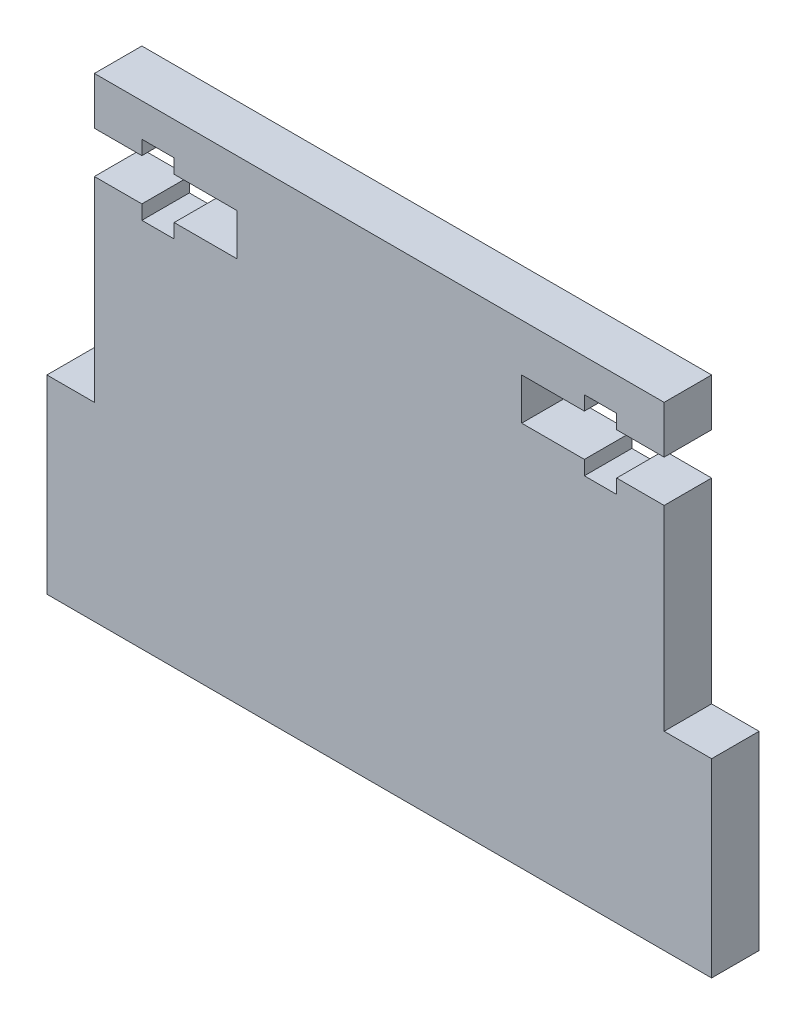
SolidWorks part; units mm, degrees
ref_plane "Front Plane" through (0, 0, 0) normal (0, 0, 1) x (1, 0, 0)
ref_plane "Top Plane" through (0, 0, 0) normal (0, 1, 0) x (1, 0, 0)
ref_plane "Right Plane" through (0, 0, 0) normal (1, 0, 0) x (0, 0, -1)
sketch "Sketch1" plane through (0, 0, 0) normal (0, 0, 1) x (1, 0, 0)
  line L1 (-30, 25) -> (30, 25)
  line L2 (-30, 25) -> (-30, -25)
  line L3 (-30, -25) -> (30, -25)
  line L4 (30, 25) -> (30, -25)
  dimension "D1" = 60
  dimension "D2" = 50
  dimension "D3" = 30
  dimension "D4" = 25
extrude "Boss-Extrude1" add sketch "Sketch1" along normal blind 5
sketch "Sketch5" plane through (0, 0, 5) normal (0, 0, 1) x (1, 0, 0)
  line L14 (-30, 17.8) -> (-13.6039, 17.8) construction
  line L26 (0, 0) -> (-23.656, 0) construction
  line L27 (0, 0) -> (0, 19.5594) construction
  line L28 (-30, 15.6) -> (-30, 20)
  line L52 (30, 20) -> (25, 20)
  line L53 (25, 20) -> (25, 21.5)
  line L54 (25, 21.5) -> (21.6, 21.5)
  line L55 (21.6, 21.5) -> (21.6, 20)
  line L56 (21.6, 20) -> (15, 20)
  line L57 (15, 20) -> (15, 15.6)
  line L58 (15, 15.6) -> (21.6, 15.6)
  line L59 (21.6, 15.6) -> (21.6, 14.1)
  line L60 (21.6, 14.1) -> (25, 14.1)
  line L61 (25, 14.1) -> (25, 15.6)
  line L62 (25, 15.6) -> (30, 15.6)
  line L63 (30, 15.6) -> (30, 20)
  line L64 (30, 17.8) -> (13.6039, 17.8) construction
  line L65 (-25, 15.6) -> (-30, 15.6)
  line L66 (-25, 14.1) -> (-25, 15.6)
  line L67 (-21.6, 14.1) -> (-25, 14.1)
  line L68 (-21.6, 15.6) -> (-21.6, 14.1)
  line L69 (-15, 15.6) -> (-21.6, 15.6)
  line L70 (-15, 20) -> (-15, 15.6)
  line L71 (-21.6, 20) -> (-15, 20)
  line L72 (-21.6, 21.5) -> (-21.6, 20)
  line L73 (-25, 21.5) -> (-21.6, 21.5)
  line L74 (-25, 20) -> (-25, 21.5)
  line L75 (-30, 20) -> (-25, 20)
  dimension "D1" = 4.4
  dimension "D2" = 3.4
  dimension "D3" = 5
  dimension "D4" = 6.6
  dimension "D5" = 1.5
  dimension "D6" = 1.5
extrude "Cut-Extrude1" cut sketch "Sketch5" against normal blind 5
sketch "Sketch6" plane through (0, 0, 0) normal (0, 0, -1) x (-1, 0, 0)
  line L0 (0, -25) -> (0, 34.8388) construction
  line L1 (-30, -25) -> (-35, -25)
  line L2 (-30, -25) -> (-30, -5)
  line L3 (-30, -5) -> (-35, -5)
  line L4 (-35, -25) -> (-35, -5)
  line L5 (30, -25) -> (-30, -25) construction
  line L7 (30, -25) -> (35, -25)
  line L8 (30, -25) -> (30, -5)
  line L9 (30, -5) -> (35, -5)
  line L10 (35, -25) -> (35, -5)
  dimension "D1" = 20
  dimension "D2" = 5
  dimension "D3" = 5
  dimension "D4" = 20
extrude "Boss-Extrude2" add sketch "Sketch6" against normal blind 5
